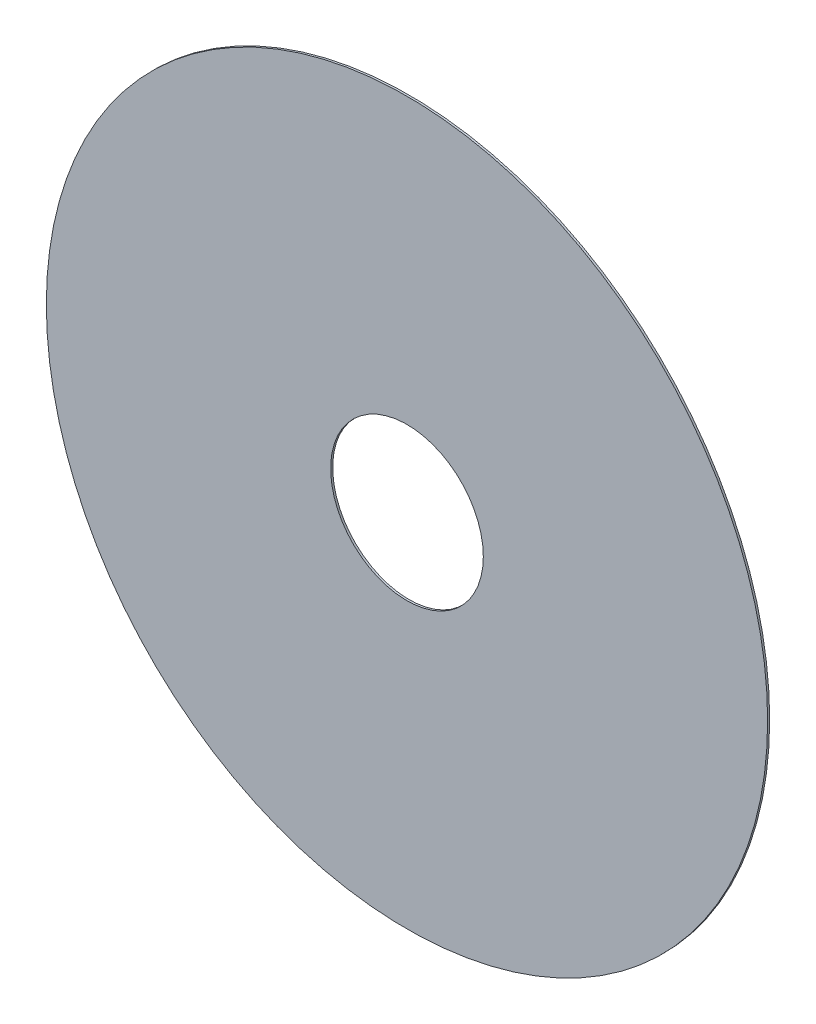
SolidWorks part; units mm, degrees
ref_plane "Front Plane" through (0, 0, 0) normal (0, 0, 1) x (1, 0, 0)
ref_plane "Top Plane" through (0, 0, 0) normal (0, 1, 0) x (1, 0, 0)
ref_plane "Right Plane" through (0, 0, 0) normal (1, 0, 0) x (0, 0, -1)
sketch "Sketch1" plane through (0, 0, 0) normal (0, 0, 1) x (1, 0, 0)
  circle A0 centre (0, 0) radius 18
  circle A1 centre (0, 0) radius 3.81
  dimension "D1" = 36
  dimension "D2" = 7.62
extrude "Boss-Extrude1" add sketch "Sketch1" along normal blind 0.1016
